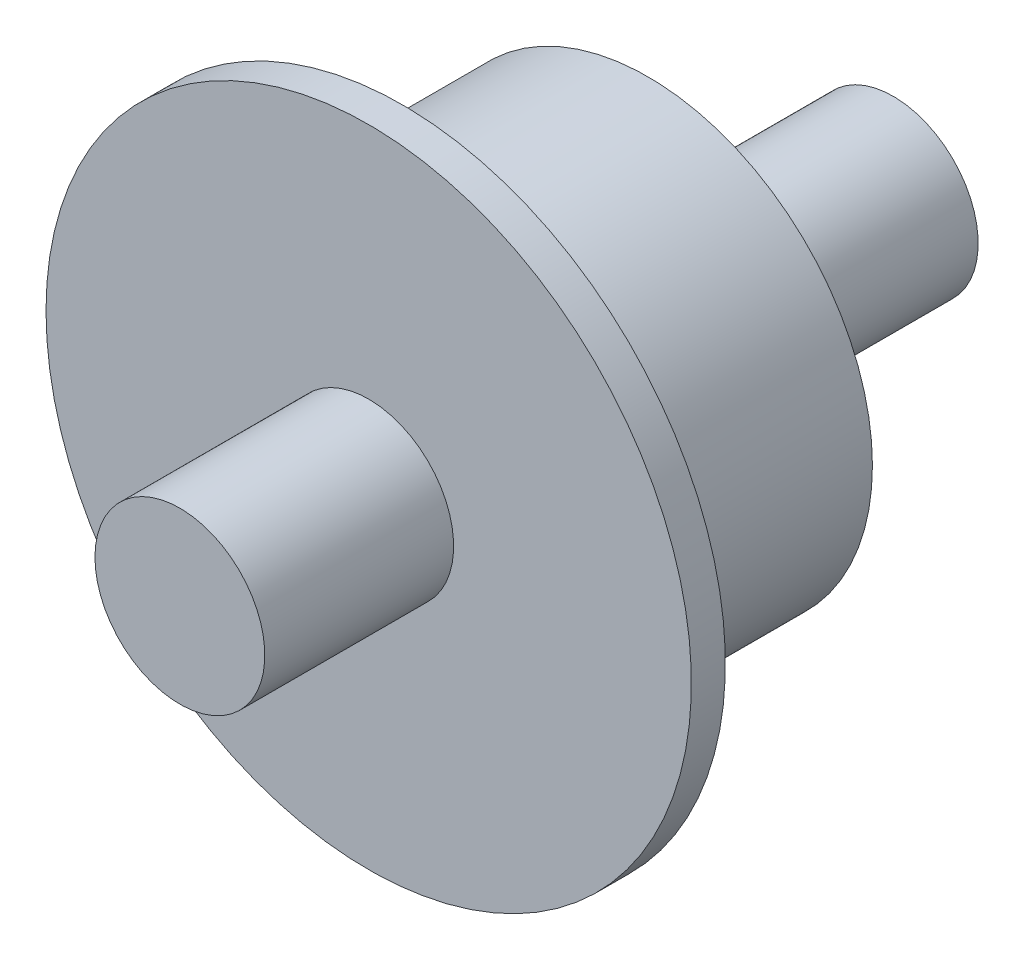
SolidWorks part; units mm, degrees
ref_plane "Front Plane" through (0, 0, 0) normal (0, 0, 1) x (1, 0, 0)
ref_plane "Top Plane" through (0, 0, 0) normal (0, 1, 0) x (1, 0, 0)
ref_plane "Right Plane" through (0, 0, 0) normal (1, 0, 0) x (0, 0, -1)
sketch "Sketch1" plane through (0, 0, 0) normal (0, 1, 0) x (1, 0, 0)
  line L0 (0, 18.8656) -> (0, -23.1344) construction
  line L1 (-5, 18.8656) -> (0, 18.8656)
  line L2 (-19, -11.0164) -> (19, -11.0164) construction
  line L3 (-19, -12.0164) -> (-19, -10.0164)
  line L4 (0, -23.1344) -> (-5, -23.1344)
  line L5 (-19, -12.0164) -> (-5, -12.0164)
  line L6 (-5, -12.0164) -> (-5, -23.1344)
  line L7 (0, 18.8656) -> (0, -23.1344)
  line L8 (-5, 18.8656) -> (-5, 4.4246)
  line L9 (-13.2163, -10.0164) -> (-19, -10.0164)
  line L10 (-5, 4.4246) -> (-13.2163, 4.4246)
  line L11 (-13.2163, 4.4246) -> (-13.2163, -10.0164)
  point P6 (0, 18.8656)
  point P9 (0, -11.0164)
  point P12 (-19, -11.0164)
  dimension "D1" = 42
  dimension "D3" = 38
  dimension "D4" = 2
  dimension "D5" = 5
revolve "Revolve1" add sketch "Sketch1" angle 360 about L7
